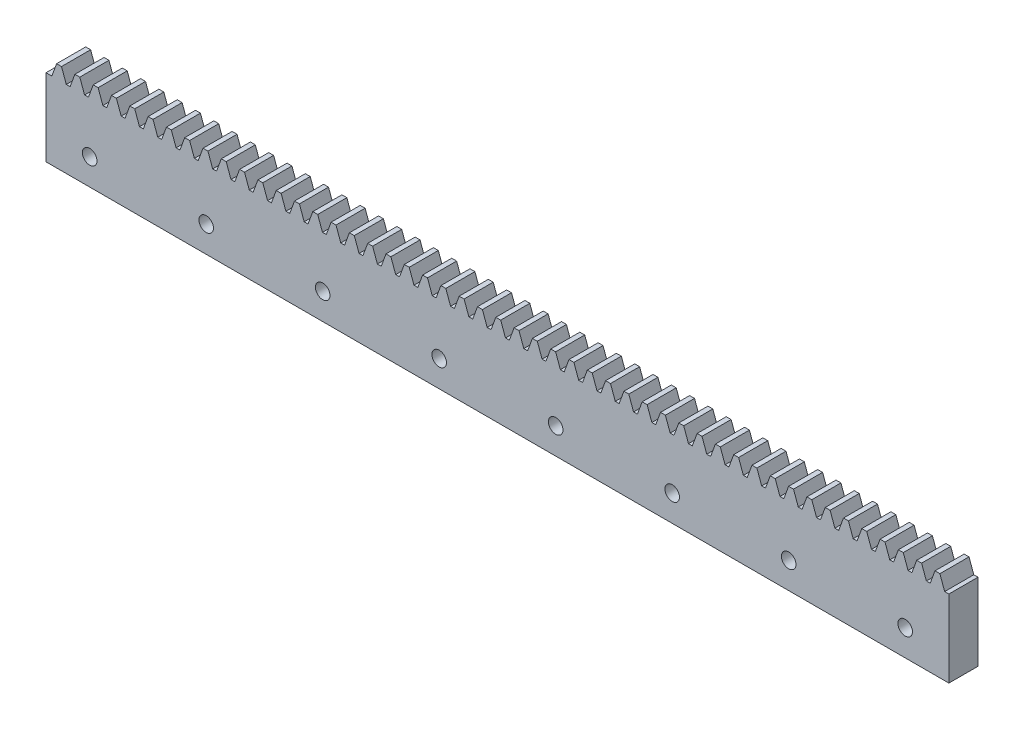
SolidWorks part; units mm, degrees
material "5052-O"
ref_plane "前基準面" through (0, 0, 0) normal (0, 0, 1) x (1, 0, 0)
ref_plane "上基準面" through (0, 0, 0) normal (0, 1, 0) x (1, 0, 0)
ref_plane "右基準面" through (0, 0, 0) normal (1, 0, 0) x (0, 0, -1)
sketch "草圖1" plane through (0, 0, 0) normal (0, 0, 1) x (1, 0, 0)
  line L1 (-77.5, -4.5) -> (77.5, -4.5)
  line L2 (-77.5, -4.5) -> (-77.5, 4.5)
  line L3 (-77.5, 4.5) -> (77.5, 4.5)
  line L4 (77.5, -4.5) -> (77.5, 4.5)
  line L5 (-77.5, -4.5) -> (77.5, 4.5) construction
  line L6 (-77.5, 4.5) -> (77.5, -4.5) construction
  point P0 (0, 0)
  dimension "D1" = 155
  dimension "D2" = 9
extrude "填料-伸長1" add sketch "草圖1" along normal blind 5
sketch "草圖3" plane through (0, 4.5, 0) normal (0, 1, 0) x (1, 0, 0)
  line L4 (77.5, 0) -> (-77.5, 0)
  line L5 (-77.5, 0) -> (-77.5, -5)
  line L6 (-77.5, -5) -> (77.5, -5)
  line L7 (77.5, -5) -> (77.5, 0)
  line L8 (77.5, 0) -> (-77.5, 0)
  line L9 (-77.5, 0) -> (-77.5, -5)
  line L10 (-77.5, -5) -> (77.5, -5)
  line L11 (77.5, -5) -> (77.5, 0)
  dimension "D1" = 0
extrude "填料-伸長2" add sketch "草圖3" along normal blind 4.25
sketch "草圖4" plane through (0, 0, 0) normal (0, 0, 1) x (1, 0, 0)
  line L0 (-76.5, 8.75) -> (-74.0193, 8.75)
  line L1 (-77.5, 8.75) -> (77.5, 8.75) construction
  line L2 (-74.0193, 8.75) -> (-74.8382, 11)
  line L3 (-74.8382, 11) -> (-75.6811, 11)
  line L4 (-75.6811, 11) -> (-76.5, 8.75)
  line L5 (-76.045, 10) -> (-74.4742, 10) construction
  dimension "D1" = 2.25
  dimension "D2" = 1
  dimension "D3" = 40
  dimension "D4" = 1
  dimension "D5" = 1.5708
extrude "填料-伸長3" add sketch "草圖4" along normal through all
hole_wizard "M3x0.5 螺紋孔1" positions "草圖5" profile "草圖6" tap size "M3x0.5" standard "Ansi Metric" end condition through all
sketch "草圖5" plane through (0, 0, 5) normal (0, 0, 1) x (1, 0, 0)
  line L0 (0, 0) -> (-70, 0) construction
  line L1 (-77.5, 8.75) -> (-77.5, -4.5) construction
  point P2 (-70, 0)
  dimension "D1" = 7.5
sketch "草圖6" plane through (-70, 0, 5) normal (1, 0, 0) x (0, -1, 0)
  line L0 (0, 0) -> (0, 5)
  line L1 (0, 5) -> (1.25, 5)
  line L2 (1.25, 5) -> (1.25, 0)
  line L5 (1.25, 0) -> (0, 0)
  line L11 (0, -6.35) -> (0, 107.95) construction
  dimension "貫穿螺孔鑽直徑" = 2.5
  dimension "貫穿螺孔鑽深度" = 5
pattern_linear "直線複製排列1" count 49 spacing 3.1416 along (1, 0, 0) of "填料-伸長3"
pattern_linear "直線複製排列2" count 8 spacing 20 along (1, 0, 0) of "M3x0.5 螺紋孔1"
equation "\"M\"= 1"
equation "\"D1@草圖4\"=\"M\"*2.25"
equation "\"D2@草圖4\"=\"M\"*1"
equation "\"D5@草圖4\"=\"M\"*PI/2"
equation "\"D3@直線複製排列1\"=\"M\"*PI"
